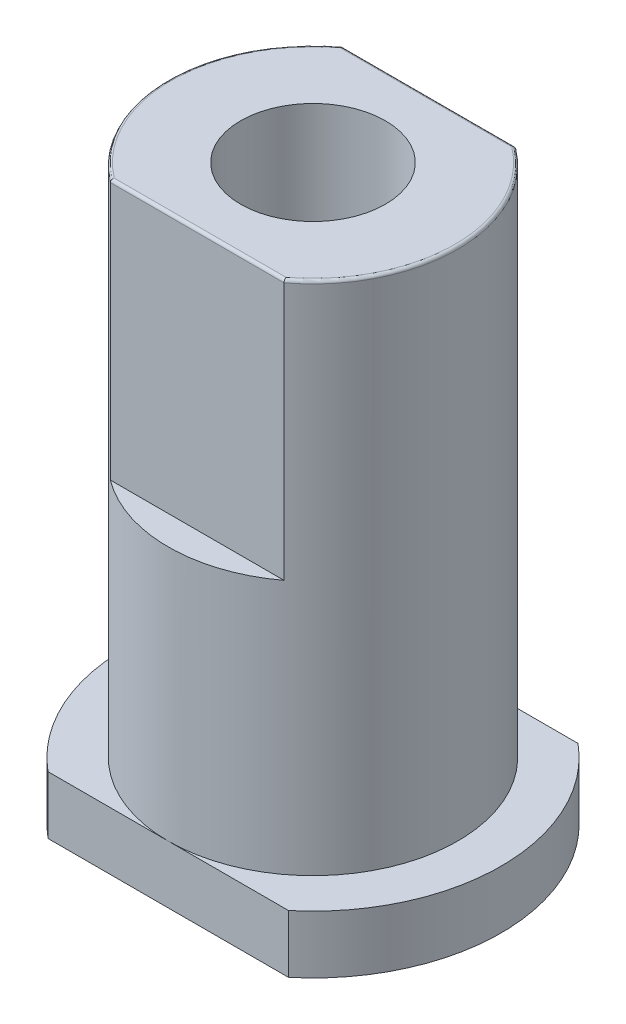
SolidWorks part; units mm, degrees
ref_plane "前视基准面" through (0, 0, 0) normal (0, 0, 1) x (1, 0, 0)
ref_plane "上视基准面" through (0, 0, 0) normal (0, 1, 0) x (1, 0, 0)
ref_plane "右视基准面" through (0, 0, 0) normal (1, 0, 0) x (0, 0, -1)
sketch "草图1" plane through (0, 0, 0) normal (0, 1, 0) x (1, 0, 0)
  circle A0 centre (0, 0) radius 5
  circle A1 centre (0, 0) radius 2.5
  dimension "D1" = 10
  dimension "D2" = 5
extrude "凸台-拉伸1" add sketch "草图1" along normal blind 17.8
sketch "草图3" plane through (0, 17.8, 0) normal (0, 1, 0) x (1, 0, 0)
  line L0 (-5, 0) -> (5, 0) construction
  line L1 (-3, -4) -> (3, -4)
  line L2 (-3, 4) -> (3, 4)
  line L3 (-5, 4) -> (5, 4) construction
  line L4 (-5, -4) -> (5, -4) construction
  circle A0 centre (0, 0) radius 5 construction
  arc A1 (-3, -4) -> (3, -4) centre (0, 0) ccw
  arc A2 (3, 4) -> (-3, 4) centre (0, 0) ccw
  dimension "D1" = 4
  dimension "D2" = 4
extrude "切除-拉伸1" cut sketch "草图3" against normal blind 9
sketch "草图4" plane through (0, 0, 0) normal (0, -1, 0) x (1, 0, 0)
  line L0 (-4.1533, 5) -> (4.1533, 5)
  line L1 (-4.1533, -5) -> (4.1533, -5)
  line L2 (-8.8739, 0) -> (9.0711, 0) construction
  arc A0 (-4.1533, 5) -> (-4.1533, -5) centre (0, 0) ccw
  arc A1 (4.1533, -5) -> (4.1533, 5) centre (0, 0) ccw
  circle A2 centre (0, 0) radius 2.5 construction
  circle A3 centre (0, 0) radius 2.5
  dimension "D1" = 13
  dimension "D2" = 10
extrude "凸台-拉伸2" add sketch "草图4" along normal blind 2
fillet "圆角1" radius 0.1 4 edges at (0, 17.8, -4) (-5, 17.8, 0) (5, 17.8, 0) (0, 17.8, 4)
